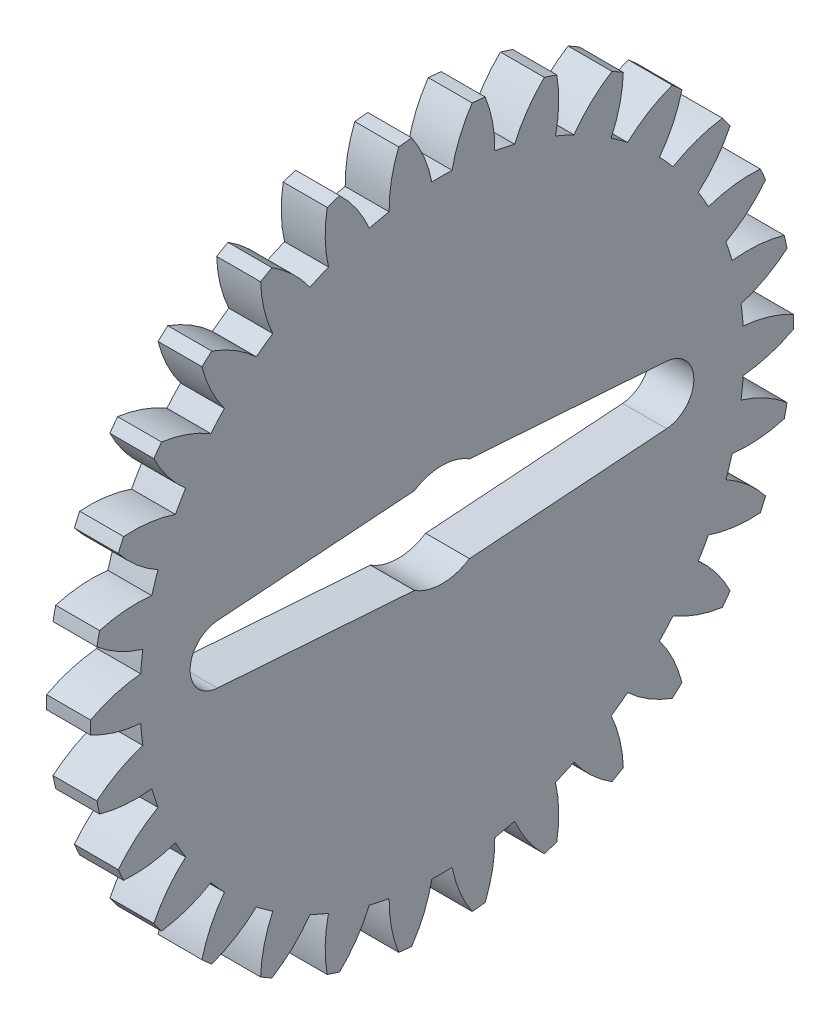
SolidWorks part; units mm, degrees
material "Acrylic (Medium-high impact)"
ref_plane "Plane1" through (0, 0, 0) normal (0, 0, 1) x (1, 0, 0)
ref_plane "Plane2" through (0, 0, 0) normal (0, 1, 0) x (1, 0, 0)
ref_plane "Plane3" through (0, 0, 0) normal (1, 0, 0) x (0, 0, -1)
other "Configuration Table"
sketch "HoldingSke" plane through (0, 0, 0) normal (0, 1, 0) x (1, 0, 0)
  line L0 (0, 0) -> (57.735, -33.3333)
  line L1 (-15, 0) -> (100, 0) construction
  line L2 (0, 0) -> (-2.1039, 2.3779)
  line L3 (0, 0) -> (-11.863, 4.5341)
  line L4 (0, 0) -> (7.479, 4.318)
  line L5 (0, 0) -> (-46.8476, -17.4728)
  line L6 (0, 0) -> (-4.1448, -2.7965)
  line L7 (-2.1039, 2.3779) -> (8.6588, 51.2068)
  line L8 (-76.2, 54.61) -> (-75.5, 54.61)
  line L9 (-71.009, 38.7566) -> (-53.1078, 45.2721)
  line L10 (-76.2, 71.12) -> (104.1128, 71.12)
  line L11 (0, 0) -> (-5, 0)
  line L12 (-76.2, 101.6) -> (-76.147, 101.6)
  line L13 (24.9733, 27.94) -> (52.9518, 28.4284)
  line L14 (24.9733, 27.94) -> (24.9743, 27.94)
  line L15 (24.9733, 27.94) -> (100.4006, 29.5858)
  line L16 (-63.627, -1.5) -> (-12.827, -1.5)
  circle A0 centre (0, 0) radius 2
  circle A1 centre (0, 0) radius 20.624
  circle A2 centre (0, 0) radius 37.5
  circle A3 centre (0, 0) radius 2
  dimension "MHD" = 41.248
  dimension "Hub_dia" = 75
  dimension "Bore" = 4
  dimension "MBD" = 4
  dimension "Num_teeth" = 30
  dimension "Pitch" = 66.6667
  dimension "Overall_len" = 50
  dimension "Show_teeth" = 30
  dimension "Thickness" = 5
  dimension "OAL" = 50.001
  dimension "T_dim" = 0.7
  dimension "Ap" = 20
  dimension "H" = 19.05
  dimension "Pitch_radius" = 180.3128
  dimension "Width" = 5
  dimension "Backlash" = 0.053
  dimension "Addendum_fac" = 1
  dimension "Dedendum_fac" = 1.25
  dimension "Clearance_fac" = 0.25
  dimension "Dedendum_add" = 0.001
  dimension "Module" = 1.5
sketch "BasProSke" plane through (0, 0, 0) normal (0, 1, 0) x (1, 0, 0)
  line L0 (-10, 0) -> (60, 0) construction
  line L1 (0, 0) -> (0, 24)
  line L2 (0, 0) -> (3, 0)
  line L3 (3, 0) -> (3, 24)
  line L4 (3, 24) -> (0, 24)
  dimension "Diameter" = 48
  dimension "D1" = 3
revolve "Base-Revolve" add sketch "BasProSke" angle 360 about L0
sketch "TooCutSke" plane through (0, 0, 0) normal (1, 0, 0) x (0, 0, -1)
  line L1 (0, 0) -> (0, 107) construction
  line L2 (0, 0) -> (-1.2703, 22.4641) construction
  line L3 (0, 0) -> (-4.6983, 44.7014) construction
  line L4 (-1.2703, 22.4641) -> (-2.3492, 22.3507) construction
  arc A0 (0.6933, 20.6123) -> (-0.6933, 20.6123) centre (0, 0) ccw
  arc A1 (2.232, 24.1511) -> (-2.232, 24.1511) centre (0, 0) ccw
  circle A2 centre (0, 0) radius 22.5 construction
  circle A3 centre (0, 0) radius 21.1431 construction
  arc A4 (-0.6933, 20.6123) -> (-2.232, 24.1511) centre (-9.5243, 18.8764) ccw
  arc A5 (2.232, 24.1511) -> (0.6933, 20.6123) centre (9.5243, 18.8764) ccw
  dimension "Root_dia" = 41.248
  dimension "Overcut_dia" = 48.508
  dimension "Pitch_dia" = 45
  dimension "Base_dia" = 42.2862
  dimension "Flank_rad" = 9
  dimension "Half_ang" = 6
  dimension "Half_CT" = 1.0848
extrude "ToothCut" cut sketch "TooCutSke" along normal through all
fillet "Breaks" [suppressed] radius 0.03
fillet "RootFillets" [suppressed] radius 0.376
pattern_circular "TeethCuts" count 30 every 12 about axis through (-10, 0, 0) along (1, 0, 0) of "ToothCut", "RootFillets", "Breaks"
sketch "HubNeaOneSke" plane through (0, 0, 0) normal (-1, 0, 0) x (0, 0, 1)
  circle A0 centre (0, 0) radius 20.624
  dimension "Diameter" = 41.248
extrude "HubNearOne" [suppressed] add sketch "HubNeaOneSke" along normal blind 45.0005
sketch "HubNeaBotSke" plane through (0, 0, 0) normal (-1, 0, 0) x (0, 0, 1)
  circle A0 centre (0, 0) radius 20.624
  dimension "Diameter" = 41.248
extrude "HubNearBoth" [suppressed] add sketch "HubNeaBotSke" along normal blind 22.5003
ref_plane "FarPln" through (5, 0, 0) normal (1, 0, 0) x (0, 0, -1)
sketch "HubFarSke" plane through (5, 0, 0) normal (1, 0, 0) x (0, 0, -1)
  circle A0 centre (0, 0) radius 20.624
  dimension "Diameter" = 41.248
extrude "HubFar" [suppressed] add sketch "HubFarSke" along normal blind 22.5003
sketch "BorSke" plane through (0, 0, 0) normal (1, 0, 0) x (0, 0, -1)
  circle A0 centre (0, 0) radius 2
  dimension "Diameter" = 4
extrude "Bore" cut sketch "BorSke" along normal mid plane 100.002
sketch "KeySke" plane through (0, 0, 0) normal (1, 0, 0) x (0, 0, -1)
  line L0 (-0.8, 0) -> (-0.8, 2.7)
  line L1 (-0.8, 2.7) -> (0.8, 2.7)
  line L2 (0.8, 2.7) -> (0.8, 0)
  line L3 (0, 0) -> (0, 34) construction
  line L4 (-0.8, 0) -> (0.8, 0)
  dimension "Offset" = 2.7
  dimension "Width" = 1.6
extrude "Keyway" [suppressed] cut sketch "KeySke" along normal mid plane 100.002
pattern_circular "Keyway2" [suppressed] count 2 every 90 about axis through (-10, 0, 0) along (1, 0, 0)
sketch "Sketch2" plane through (0, 0, 0) normal (-1, 0, 0) x (0, 0, 1)
  line L2 (0, 3.3151) -> (0, -3.3151) construction
  line L5 (-1.8835, 2.95) -> (-15.3416, 1.995)
  line L6 (-15.3416, -1.995) -> (-1.8835, -2.95)
  line L7 (15.3416, -1.995) -> (1.8835, -2.95)
  line L8 (1.8835, 2.95) -> (15.3416, 1.995)
  arc A2 (-1.8835, -2.95) -> (1.8835, -2.95) centre (0, 0) ccw
  arc A3 (-15.3416, 1.995) -> (-15.3416, -1.995) centre (-15.2, 0) ccw
  arc A5 (15.3416, 1.995) -> (15.3416, -1.995) centre (15.2, 0) cw
  arc A7 (-15.3416, -1.995) -> (-15.3416, 1.995) centre (-15.2, 0) ccw construction
  arc A8 (-1.8835, 2.95) -> (-1.8835, -2.95) centre (0, 0) ccw construction
  arc A9 (1.8835, -2.95) -> (1.8835, 2.95) centre (0, 0) ccw construction
  arc A10 (1.8835, 2.95) -> (-1.8835, 2.95) centre (0, 0) ccw
  arc A11 (15.3416, -1.995) -> (15.3416, 1.995) centre (15.2, 0) cw construction
  dimension "D1" = 7
  dimension "D2" = 4
  dimension "D3" = 5.9
  dimension "D4" = 15.2
extrude "Cut-Extrude1" cut sketch "Sketch2" against normal through all
equation "' \"Module@HoldingSke\" = 6.35"
equation "' \"Num_teeth@HoldingSke\" = 12"
equation "' \"Ap@HoldingSke\" =  20"
equation "' \"Ap@HoldingSke\" = 20"
equation "' \"Width@HoldingSke\" = 0.5 * 25.4"
equation "' \"Hub_dia@HoldingSke\"= 1 * 25.4"
equation "' \"Hub_dia@HoldingSke\" = 1 * 25.4"
equation "' \"Overall_len@HoldingSke\" = 1.0 * 25.4"
equation "' \"Bore@HoldingSke\" = 0.75 * 25.4"
equation "' \"T_dim@HoldingSke\" = 0.1 * 25.4"
equation "' \"Width@KeySke\" = 0.25 * 25.4"
equation "' \"Show_teeth@HoldingSke\" = 13"
equation "' \"Backlash@HoldingSke\" = 0.009 * 25.4"
equation "' \"Addendum_fac@HoldingSke\" = 1.0"
equation "' \"Dedendum_fac@HoldingSke\" = 1.25"
equation "' \"Dedendum_add@HoldingSke\" = 0.00005 * 25.4"
equation "' \"Clearance_fac@HoldingSke\" = 0.25"
equation "\"Pitch@HoldingSke\" = 1 / \"Module@HoldingSke\""
equation "\"Overcut_dia@TooCutSke\" = (\"Num_teeth@HoldingSke\" + 2 * \"Addendum_fac@HoldingSke\") / \"Pitch@HoldingSke\" + 0.002 * 25.4"
equation "\"Pitch_dia@TooCutSke\" = \"Num_teeth@HoldingSke\" / \"Pitch@HoldingSke\""
equation "\"Base_dia@TooCutSke\" = \"Num_teeth@HoldingSke\" / \"Pitch@HoldingSke\" * cos((\"Ap@HoldingSke\"  * 3.14159265 / 180))"
equation "\"Root_dia@TooCutSke\" = (\"Num_teeth@HoldingSke\" + 2) / \"Pitch@HoldingSke\" - 2 * (\"Addendum_fac@HoldingSke\" + \"Dedendum_fac@HoldingSke\") / \"Pitch@HoldingSke\" - \"Dedendum_add@HoldingSke\" * 2"
equation "\"Half_ang@TooCutSke\" = 180 / \"Num_teeth@HoldingSke\""
equation "\"Half_CT@TooCutSke\" = \"Num_teeth@HoldingSke\" / \"Pitch@HoldingSke\" * sin((3.14159265 / 2 / \"Num_teeth@HoldingSke\")) / 2 - 7 * \"Backlash@HoldingSke\" / 4"
equation "\"Flank_rad@TooCutSke\" = \"Num_teeth@HoldingSke\" / \"Pitch@HoldingSke\" / 5"
equation "\"Radius@RootFillets\" = \"Clearance_fac@HoldingSke\" / \"Pitch@HoldingSke\" + \"Dedendum_add@HoldingSke\""
equation "\"Break_rad@Breaks\" = 0.02 / \"Pitch@HoldingSke\""
equation "\"Thickness@HoldingSke\" = \"Width@HoldingSke\""
equation "\"OAL@HoldingSke\" = \"Thickness@HoldingSke\""
equation "\"MHD@HoldingSke\" = (\"Num_teeth@HoldingSke\" + 2) / \"Pitch@HoldingSke\" - 2 * (\"Addendum_fac@HoldingSke\" + \"Dedendum_fac@HoldingSke\")  / \"Pitch@HoldingSke\" - \"Dedendum_add@HoldingSke\" * 2"
equation "\"MBD@HoldingSke\" = (\"Num_teeth@HoldingSke\" + 2) / \"Pitch@HoldingSke\" - 2 * (\"Addendum_fac@HoldingSke\" + \"Dedendum_fac@HoldingSke\")  / \"Pitch@HoldingSke\" - \"Dedendum_add@HoldingSke\" * 2 - 0.002 * 25.4"
equation "\"MHD@HoldingSke\" = ((sgn( \"MHD@HoldingSke\" - \"Hub_dia@HoldingSke\" )-1)*( \"MHD@HoldingSke\" - \"Hub_dia@HoldingSke\" ))/-2+ \"Hub_dia@HoldingSke\""
equation "\"MBD@HoldingSke\" = ((sgn( \"MBD@HoldingSke\" - \"Bore@HoldingSke\" )-1)*( \"MBD@HoldingSke\" - \"Bore@HoldingSke\" ))/-2+ \"Bore@HoldingSke\""
equation "\"OAL@HoldingSke\" = ((sgn( \"OAL@HoldingSke\" - \"Overall_len@HoldingSke\" )+1)*( \"OAL@HoldingSke\" - \"Overall_len@HoldingSke\" ))/2 + \"Overall_len@HoldingSke\" + 0.000002 * 25.4"
equation "\"Num_teeth@TeethCuts\" = int( \"Show_teeth@HoldingSke\" ) + 1"
equation "\"Num_teeth@TeethCuts\" = ((sgn( \"Num_teeth@TeethCuts\" - \"Num_teeth@HoldingSke\" )-1)*( \"Num_teeth@TeethCuts\" - \"Num_teeth@HoldingSke\" ))/-2+ \"Num_teeth@HoldingSke\""
equation "\"Num_teeth@TeethCuts\" = ((sgn( \"Num_teeth@TeethCuts\" - 2.0)+1)*( \"Num_teeth@TeethCuts\" - 2.0))/2 +2.0"
equation "\"Angle@TeethCuts\" = 360.0 / \"Num_teeth@HoldingSke\""
equation "\"Diameter@BasProSke\" = (\"Num_teeth@HoldingSke\" + 2 * \"Addendum_fac@HoldingSke\") / \"Pitch@HoldingSke\""
equation "' \"Fillet_rad@BasProSke\" =  \"Thickness@HoldingSke\" * 0.05"
equation "' \"Fillet_rad@BasProSke\" = \"Thickness@HoldingSke\" * 0.05"
equation "\"MHD@HoldingSke\" = ((sgn( \"MHD@HoldingSke\" - \"Root_dia@TooCutSke\" )-1)*( \"MHD@HoldingSke\" - \"Root_dia@TooCutSke\" ))/-2+ \"Root_dia@TooCutSke\""
equation "\"Diameter@HubNeaOneSke\" = \"MHD@HoldingSke\""
equation "\"Diameter@HubNeaBotSke\" = \"MHD@HoldingSke\""
equation "\"Diameter@HubFarSke\" = \"MHD@HoldingSke\""
equation "\"Diameter@BorSke\" = \"MBD@HoldingSke\""
equation "\"D1@Bore\" = \"OAL@HoldingSke\" * 2.0"
equation "\"D1@Keyway\" = \"OAL@HoldingSke\" * 2.0"
equation "\"Offset@KeySke\" = \"T_dim@HoldingSke\" + \"MBD@HoldingSke\" / 2.0"
